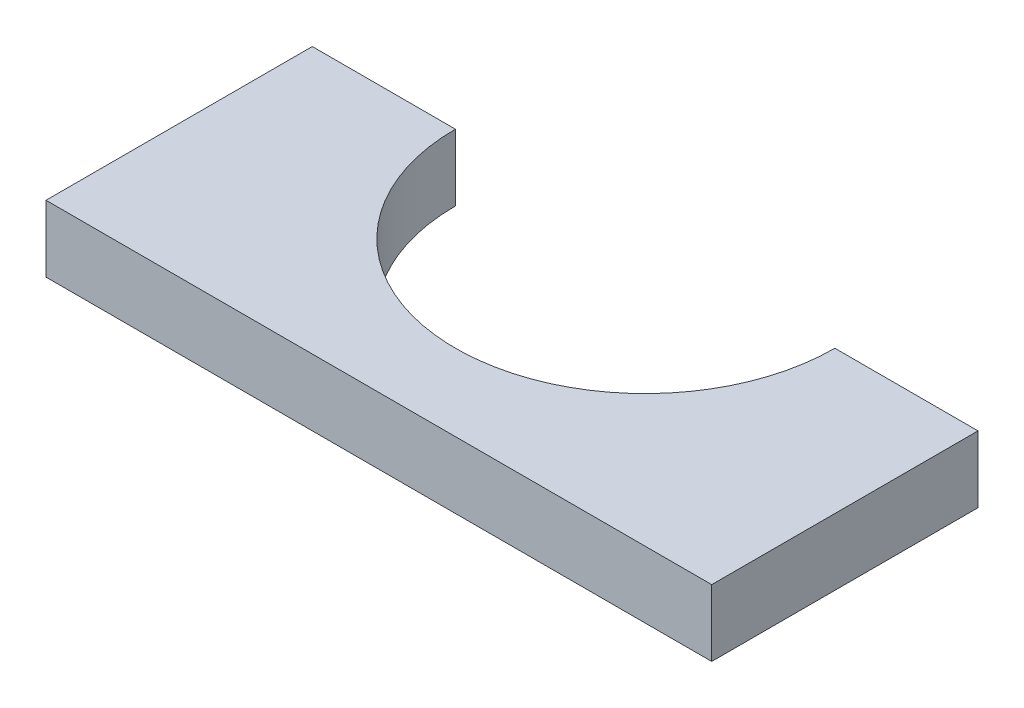
SolidWorks part; units mm, degrees
ref_plane "Спереди" through (0, 0, 0) normal (0, 0, 1) x (1, 0, 0)
ref_plane "Сверху" through (0, 0, 0) normal (0, 1, 0) x (1, 0, 0)
ref_plane "Справа" through (0, 0, 0) normal (1, 0, 0) x (0, 0, -1)
sketch "Эскиз1" plane through (0, 0, 0) normal (0, 1, 0) x (1, 0, 0)
  line L0 (-100, 0) -> (100, 0)
  line L1 (-57, 80) -> (-100, 80)
  line L2 (-100, 80) -> (-100, 0)
  line L3 (57, 80) -> (100, 80)
  line L4 (100, 80) -> (100, 0)
  arc A0 (-57, 80) -> (57, 80) centre (0, 80) ccw
  point P4 (0, 0)
extrude "Бобышка-Вытянуть1" add sketch "Эскиз1" along normal blind 20
